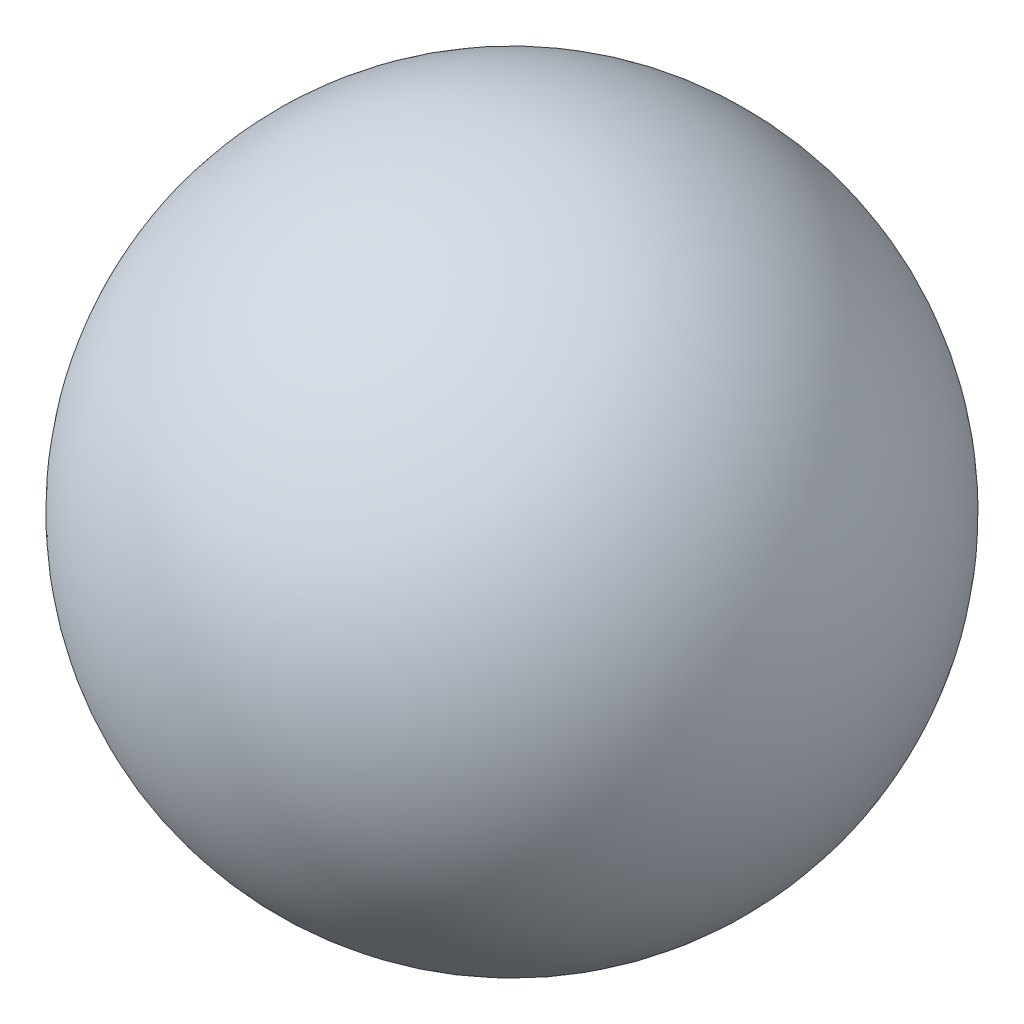
SolidWorks part; units mm, degrees
ref_plane "Alzado" through (0, 0, 0) normal (0, 0, 1) x (1, 0, 0)
ref_plane "Planta" through (0, 0, 0) normal (0, 1, 0) x (1, 0, 0)
ref_plane "Vista lateral" through (0, 0, 0) normal (1, 0, 0) x (0, 0, -1)
sketch "Croquis1" plane through (0, 0, 0) normal (0, 0, 1) x (1, 0, 0)
  line L0 (-33.6379, -23.506) -> (16.3621, -23.506)
  arc A0 (16.3621, -23.506) -> (-33.6379, -23.506) centre (-8.6379, -23.506) ccw
  dimension "D1" = 50
revolve "Revolución1" add sketch "Croquis1" angle 360 about L0
